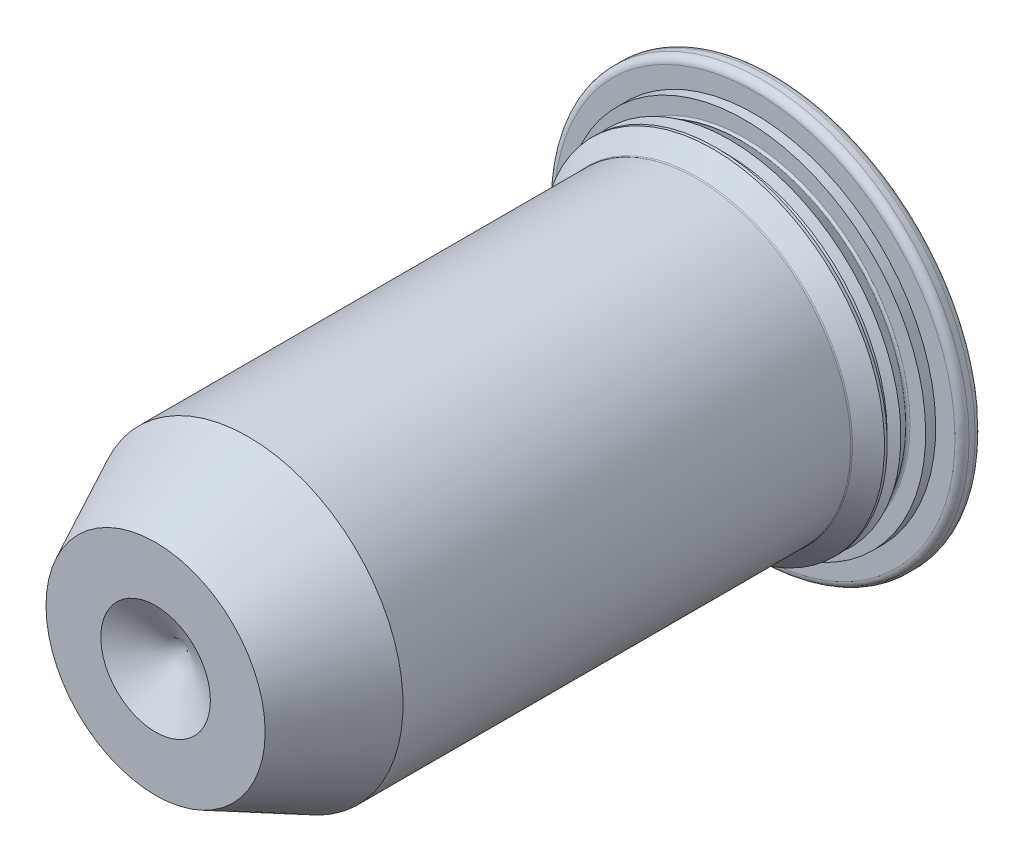
SolidWorks part; units mm, degrees
ref_plane "Front Plane" through (0, 0, 0) normal (0, 0, 1) x (1, 0, 0)
ref_plane "Top Plane" through (0, 0, 0) normal (0, 1, 0) x (1, 0, 0)
ref_plane "Right Plane" through (0, 0, 0) normal (1, 0, 0) x (0, 0, -1)
sketch "Sketch1" plane through (0, 0, 0) normal (1, 0, 0) x (0, 0, -1)
  line L0 (-6.35, 0) -> (6.35, 0) construction
  line L1 (-6.35, 2.2479) -> (-6.35, -2.2479) construction
  line L2 (6.35, 4.2545) -> (6.35, -4.2545) construction
  line L3 (-6.35, 2.2479) -> (-4.4492, 3.175) construction
  line L4 (-6.35, -2.2479) -> (-4.4492, -3.175) construction
  point P4 (0, 0)
  point P8 (-6.35, 0)
  point P11 (6.35, 0)
  dimension "Diameter" = 6.35
  dimension "Length" = 12.7
  dimension "Tip Diameter" = 4.4958
  dimension "Head Diameter" = 8.509
  dimension "D1" = 64
sketch "Sketch2" plane through (0, 0, 0) normal (1, 0, 0) x (0, 0, -1)
  line L0 (-6.35, 0) -> (6.35, 0)
  line L1 (-6.35, 2.2479) -> (-6.35, 0)
  line L4 (6.35, 0) -> (6.35, 4.1105)
  line L5 (6.206, 4.2545) -> (6.082, 4.2545)
  line L6 (5.938, 4.1105) -> (5.938, 3.7147)
  line L7 (5.938, 3.7147) -> (5.732, 3.7147)
  line L8 (5.732, 3.7147) -> (5.732, 3.514)
  line L9 (5.732, 3.514) -> (5.425, 3.514)
  line L10 (5.425, 3.514) -> (5.331, 3.3259)
  line L11 (5.239, 3.3259) -> (5.145, 3.514)
  line L12 (5.145, 3.514) -> (5.089, 3.514)
  line L13 (5.089, 3.514) -> (4.75, 3.175)
  line L14 (4.75, 3.175) -> (-4.4492, 3.175)
  line L15 (-4.4492, 3.175) -> (-6.35, 2.2479)
  arc A2 (6.35, 4.1105) -> (6.206, 4.2545) centre (6.206, 4.1105) ccw
  arc A3 (6.082, 4.2545) -> (5.938, 4.1105) centre (6.082, 4.1105) ccw
  arc A4 (5.239, 3.3259) -> (5.331, 3.3259) centre (5.285, 3.4056) ccw
  point P17 (6.35, 0)
  dimension "D5" = 0.144
  dimension "D11" = 0.092
  dimension "D1" = 135
  dimension "D2" = 53.13
  dimension "D3" = 1.6
  dimension "D4" = 0.412
  dimension "D6" = 0.206
  dimension "D7" = 0.307
  dimension "D8" = 0.056
  dimension "D9" = 0.5398
  dimension "D10" = 0.339
  dimension "D12" = 0.092
revolve "Revolve1" add sketch "Sketch2" angle 360 about L0
sketch "Sketch3" plane through (0, 0, 0) normal (1, 0, 0) x (0, 0, -1)
  line L0 (-6.35, 1.1239) -> (-5.7011, 0)
  line L1 (-6.35, 2.2479) -> (-6.35, -2.2479) construction
  line L2 (-6.35, 0) -> (6.35, 0) construction
  line L4 (-6.35, 0) -> (-6.35, 1.1239)
  line L5 (-6.35, 0) -> (-5.7011, 0)
  line L6 (-6.35, 0) -> (-4.4492, 0) construction
  dimension "D1" = 60
  dimension "D2" = 2.2479
revolve "Cut-Revolve1" cut sketch "Sketch3" angle 360 about L6
sketch "Sketch4" plane through (0, 0, 0) normal (1, 0, 0) x (0, 0, -1)
  line L0 (5.425, 3.514) -> (5.732, 3.3259)
  line L1 (5.732, 3.514) -> (5.732, -3.514) construction
  line L2 (5.732, 3.3259) -> (5.732, 3.514)
  line L3 (5.732, 3.7147) -> (5.732, -3.7147) construction
  line L4 (5.732, 3.514) -> (5.425, 3.514)
revolve "Cut-Revolve2" cut sketch "Sketch4" angle 360 about L0
fillet "Fillet1" radius 0.0381 2 edges at (0, -3.3259, -5.732) (0, -3.175, -4.75)
equation "\"D2@Sketch3\"=\"Tip Diameter@Sketch1\"*.5"
equation "\"D9@Sketch2\"=(\"Head Diameter@Sketch1\"-\"Diameter@Sketch1\")*.25"
equation "\"D10@Sketch2\"=(\"Head Diameter@Sketch1\"-\"Diameter@Sketch1\")*.157"
